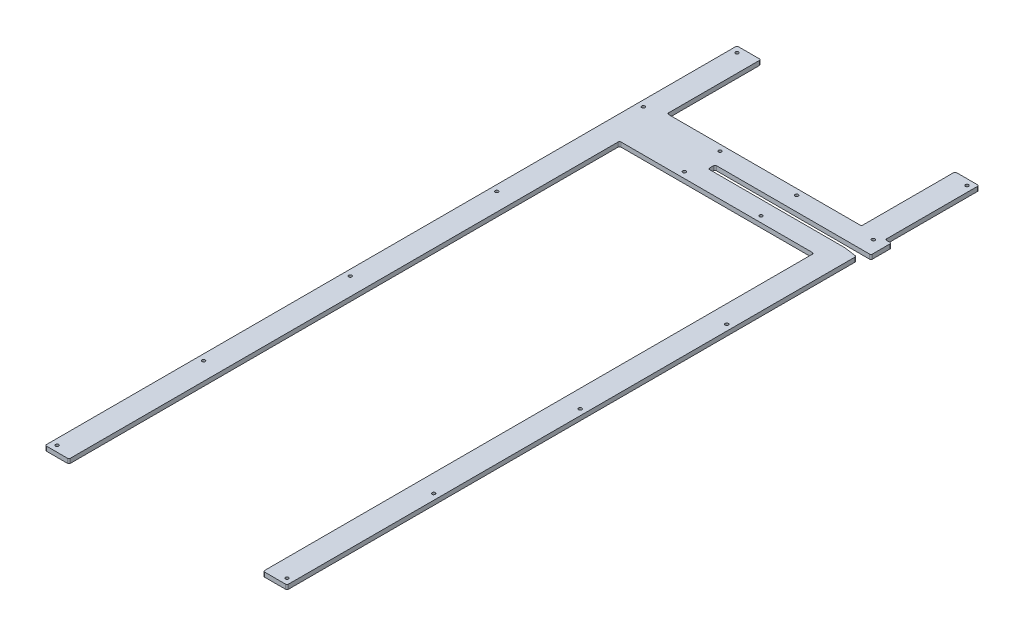
SolidWorks part; units mm, degrees
material "PE Low/Medium Density"
ref_plane "Front Plane" through (0, 0, 0) normal (0, 0, 1) x (1, 0, 0)
ref_plane "Top Plane" through (0, 0, 0) normal (0, 1, 0) x (1, 0, 0)
ref_plane "Right Plane" through (0, 0, 0) normal (1, 0, 0) x (0, 0, -1)
sketch "Sketch1" plane through (0, 0, 0) normal (0, 1, 0) x (1, 0, 0)
  line L0 (-258.3, 0) -> (-207.5, 0)
  line L1 (-207.5, 0) -> (-207.5, 1176)
  line L2 (-207.5, 1176) -> (207.5, 1176)
  line L3 (207.5, 1176) -> (207.5, 0)
  line L4 (207.5, 0) -> (258.3, 0)
  line L5 (258.3, 0) -> (258.3, 1215.5149)
  line L6 (230.3, 1219.45) -> (-61.7, 1219.45)
  line L7 (-61.7, 1219.45) -> (-61.7, 1234.15)
  line L8 (-61.7, 1234.15) -> (271.3, 1234.15)
  line L9 (271.3, 1234.15) -> (271.3, 1277.6)
  line L10 (271.3, 1277.6) -> (-258.3, 1277.6)
  line L11 (-258.3, 1277.6) -> (-258.3, 0)
  line L12 (-207.5, 0) -> (207.5, 0) construction
  line L13 (-182.147, 1277.6) -> (-182.147, 1176) construction
  line L14 (-61.7, 1226.8) -> (-162.228, 1226.8) construction
  line L15 (230.3, 1219.45) -> (258.3, 1215.5149)
  point P0 (0, 0)
  point P18 (-182.147, 1226.8)
  dimension "D1" = 516.6
  dimension "D2" = 1277.6
  dimension "D3" = 50.8
  dimension "D4" = 101.6
  dimension "D5" = 14.7
  dimension "D6" = 320
  dimension "D7" = 13
  dimension "D8" = 8
  dimension "D9" = 28
extrude "Boss-Extrude1" add sketch "Sketch1" along normal blind 9.525
sketch "Sketch4" plane through (0, 0, 0) normal (0, -1, 0) x (1, 0, 0)
  line L0 (271.3, -1277.6) -> (-258.3, -1277.6) construction
  line L1 (-258.3, -1277.6) -> (-207.5, -1277.6)
  line L2 (-258.3, -1277.6) -> (-258.3, -1477.6)
  line L3 (-258.3, -1477.6) -> (-207.5, -1477.6)
  line L4 (-207.5, -1277.6) -> (-207.5, -1477.6)
  line L5 (258.3, -1277.6) -> (207.5, -1277.6)
  line L6 (258.3, -1277.6) -> (258.3, -1477.6)
  line L7 (258.3, -1477.6) -> (207.5, -1477.6)
  line L8 (207.5, -1277.6) -> (207.5, -1477.6)
  line L9 (258.3, 0) -> (258.3, -1215.5149) construction
  line L10 (207.5, -1176) -> (207.5, 0) construction
  line L11 (-207.5, 0) -> (-207.5, -1176) construction
  dimension "D1" = 200
extrude "Boss-Extrude2" add sketch "Sketch4" against normal up to surface (9.525 mm away) up to face at (49.9615, 9.525, -848.455)
hole_wizard "CSK for 1/4 Flat Head Machine Screw (100)1" positions "Sketch3" profile "Sketch2" countersink size "1/4" standard "Ansi Inch" end condition through all
sketch "Sketch3" plane through (0, 0, 0) normal (0, -1, 0) x (1, 0, 0)
  line L0 (271.3, -1277.6) -> (258.3, -1277.6) construction
  line L1 (-258.3, -1477.6) -> (-258.3, 0) construction
  point P0 (-245.6, -1264.9)
  dimension "D1" = 12.7
  dimension "D2" = 12.7
sketch "Sketch2" plane through (-245.6, 0, -1264.9) normal (1, 0, 0) x (0, 0, -1)
  line L0 (0, 0) -> (0, 9.525)
  line L1 (0, 9.525) -> (3.3782, 9.525)
  line L2 (3.3782, 9.525) -> (3.3782, 4.5682)
  line L3 (3.3782, 4.5682) -> (8.8224, 0)
  line L5 (8.8224, 0) -> (0, 0)
  line L6 (-3.3782, 4.5682) -> (-8.8224, 0) construction
  line L11 (0, -6.35) -> (0, 107.95) construction
  dimension "Thru Hole Dia." = 6.7564
  dimension "Thru Hole Depth" = 9.5251
  dimension "Near C'Sink Dia." = 17.6448
  dimension "Near C'Sink Angle" = 100
pattern_linear "LPattern1" [suppressed] count 2 spacing 491.2 count 5 spacing 287.65
pattern_linear "LPattern3" count 2 spacing 491.2 along (1, 0, 0) count 5 spacing 313.05 along (0, 0, 1) of "CSK for 1/4 Flat Head Machine Screw (100)1"
pattern_linear "LPattern2" count 3 spacing 163.7333 along (1, 0, 0) count 2 spacing 76.2 along (0, 0, 1) skipping (0, 1) of "CSK for 1/4 Flat Head Machine Screw (100)1"
hole_wizard "CSK for 1/4 Flat Head Machine Screw (100)2" positions "Sketch6" profile "Sketch5" countersink size "1/4" standard "Ansi Inch" end condition through all
sketch "Sketch6" plane through (0, 0, 0) normal (0, -1, 0) x (1, 0, 0)
  line L0 (-258.3, -1477.6) -> (-207.5, -1477.6) construction
  line L1 (-258.3, -1477.6) -> (-258.3, 0) construction
  point P0 (-245.6, -1464.9)
  dimension "D1" = 12.7
  dimension "D2" = 12.7
sketch "Sketch5" plane through (-245.6, 0, -1464.9) normal (1, 0, 0) x (0, 0, -1)
  line L0 (0, 0) -> (0, 9.525)
  line L1 (0, 9.525) -> (3.3782, 9.525)
  line L2 (3.3782, 9.525) -> (3.3782, 4.5682)
  line L3 (3.3782, 4.5682) -> (8.8224, 0)
  line L5 (8.8224, 0) -> (0, 0)
  line L6 (-3.3782, 4.5682) -> (-8.8224, 0) construction
  line L11 (0, -6.35) -> (0, 107.95) construction
  dimension "Thru Hole Dia." = 6.7564
  dimension "Thru Hole Depth" = 9.5251
  dimension "Near C'Sink Dia." = 17.6448
  dimension "Near C'Sink Angle" = 100
mirror "Mirror1" about plane through (0, 0, 0) normal (1, 0, 0) of "CSK for 1/4 Flat Head Machine Screw (100)2"
fillet "Fillet1" radius 3.175 11 edges at (258.3, 4.7625, 0) (207.5, 4.7625, 0) (-207.5, 4.7625, 0) (-258.3, 4.7625, 0) (207.5, 4.7625, -1176) (-207.5, 4.7625, -1176) (258.3, 4.7625, -1215.5149) (271.3, 4.7625, -1234.15) (271.3, 4.7625, -1277.6) (-61.7, 4.7625, -1219.45) (-61.7, 4.7625, -1234.15)
fillet "Fillet2" radius 3.175 7 edges at (207.5, 4.7625, -1477.6) (258.3, 4.7625, -1477.6) (-258.3, 4.7625, -1477.6) (-207.5, 4.7625, -1477.6) (207.5, 4.7625, -1277.6) (258.3, 4.7625, -1277.6)
